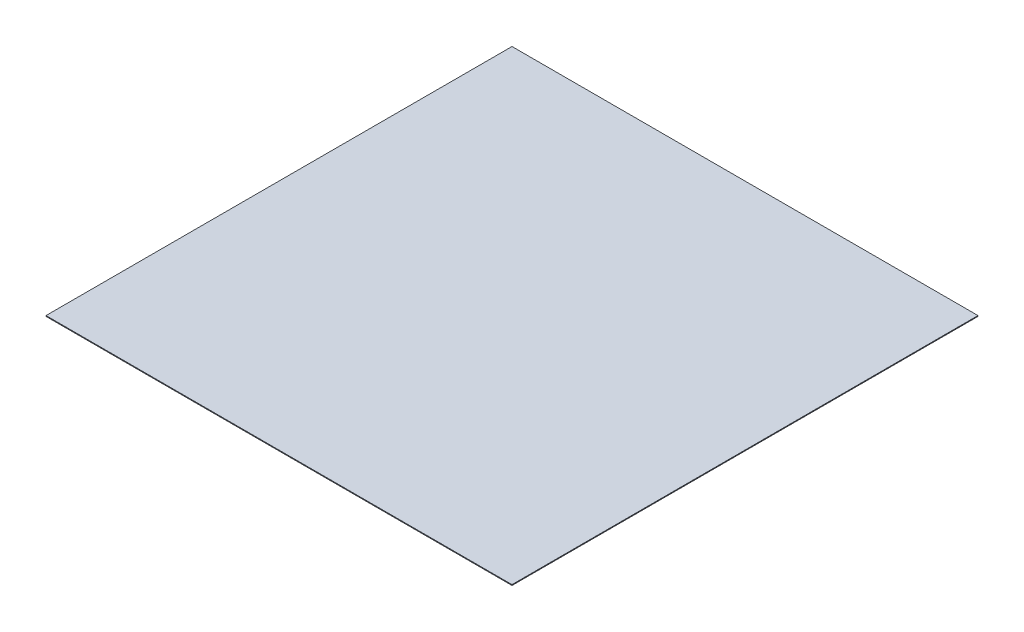
SolidWorks part; units mm, degrees
ref_plane "Front Plane" through (0, 0, 0) normal (0, 0, 1) x (1, 0, 0)
ref_plane "Top Plane" through (0, 0, 0) normal (0, 1, 0) x (1, 0, 0)
ref_plane "Right Plane" through (0, 0, 0) normal (1, 0, 0) x (0, 0, -1)
sketch "Sketch1" plane through (0, 0, 0) normal (0, 1, 0) x (1, 0, 0)
  line L1 (0, 0) -> (1524, 0)
  line L2 (0, 0) -> (0, 1524)
  line L3 (0, 1524) -> (1524, 1524)
  line L4 (1524, 0) -> (1524, 1524)
  line L5 (0, 0) -> (1524, 1524) construction
  line L6 (0, 1524) -> (1524, 0) construction
  point P4 (762, 762)
  dimension "D1" = 1524
extrude "Boss-Extrude1" add sketch "Sketch1" along normal blind 2.54
